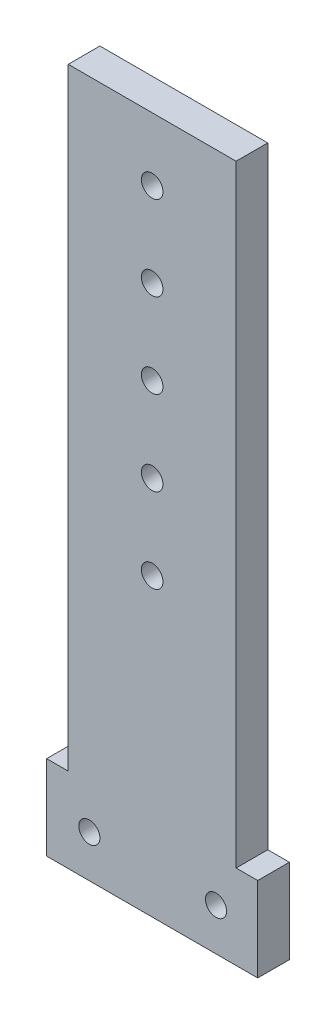
SolidWorks part; units mm, degrees
material "AISI 1020"
ref_plane "Front Plane" through (0, 0, 0) normal (0, 0, 1) x (1, 0, 0)
ref_plane "Top Plane" through (0, 0, 0) normal (0, 1, 0) x (1, 0, 0)
ref_plane "Right Plane" through (0, 0, 0) normal (1, 0, 0) x (0, 0, -1)
sketch "Sketch1" plane through (0, 0, 0) normal (0, 0, 1) x (1, 0, 0)
  line L0 (25.4, -6.35) -> (25.4, 203.2) construction
  line L2 (0.15, 19.05) -> (0.15, 203.2)
  line L3 (0.15, 203.2) -> (50.65, 203.2)
  line L4 (50.65, 19.05) -> (50.65, 203.2)
  line L5 (0.15, 19.05) -> (-6.35, 19.05)
  line L6 (-6.35, 19.05) -> (-6.35, -6.35)
  line L7 (-6.35, -6.35) -> (57.15, -6.35)
  line L8 (57.15, -6.35) -> (57.15, 19.05)
  line L9 (57.15, 19.05) -> (50.65, 19.05)
  circle A0 centre (6.5, 6.35) radius 3.175
  circle A1 centre (44.6, 6.35) radius 3.175
  circle A2 centre (25.4, 184.2) radius 3.25
  circle A3 centre (25.4, 158.8) radius 3.25
  circle A4 centre (25.4, 133.4) radius 3.25
  circle A5 centre (25.4, 108) radius 3.25
  circle A6 centre (25.4, 82.6) radius 3.25
  dimension "D1" = 6.35
  dimension "D2" = 6.35
  dimension "D7" = 6.5
  dimension "D8" = 19
  dimension "D10" = 6.5
  dimension "D11" = 6.5
  dimension "D12" = 6.5
  dimension "D13" = 6.5
  dimension "D3" = 38.1
  dimension "D4" = 6.35
  dimension "D14" = 25.4
  dimension "D15" = 25.4
  dimension "D16" = 25.4
  dimension "D17" = 25.4
  dimension "D18" = 25.4
  dimension "D19" = 6.5
  dimension "D20" = 6.5
  dimension "D22" = 25.4
extrude "Boss-Extrude1" add sketch "Sketch1" along normal blind 9.525
